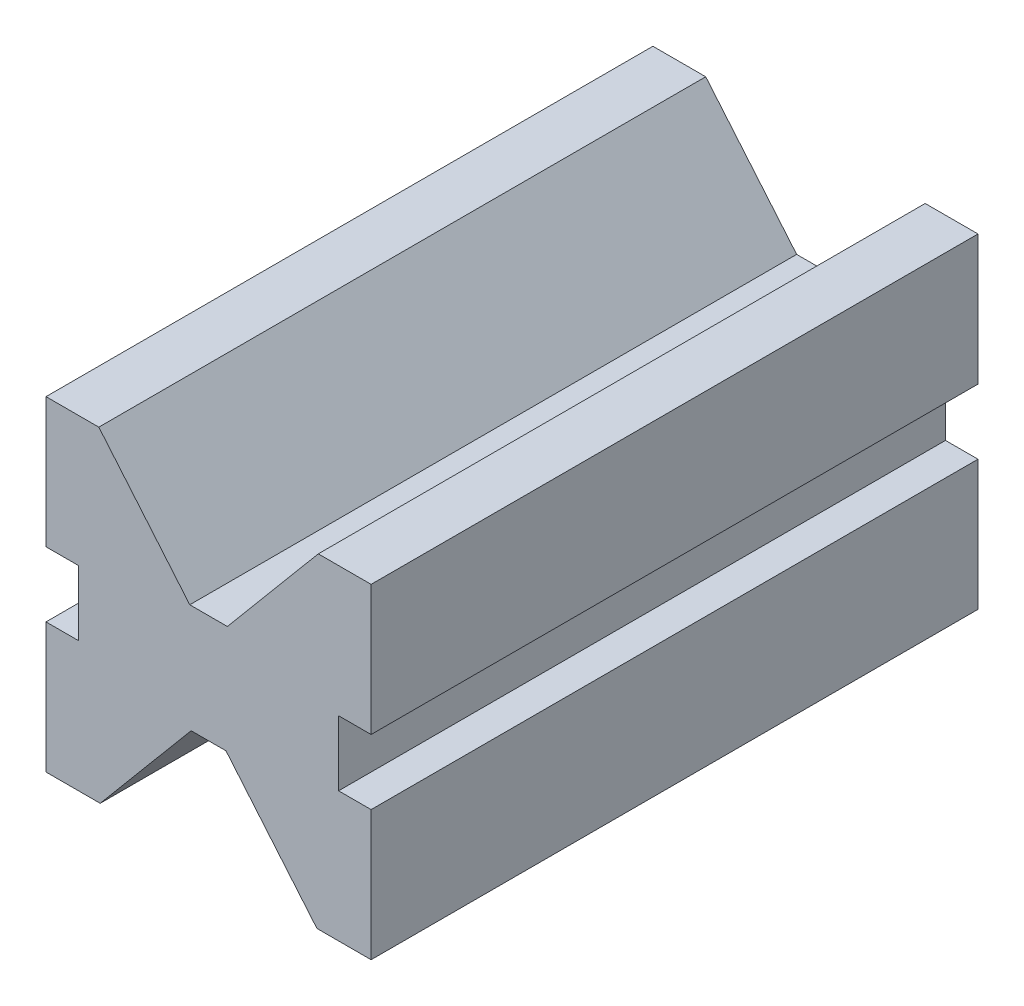
SolidWorks part; units mm, degrees
ref_plane "Front Plane" through (0, 0, 0) normal (0, 0, 1) x (1, 0, 0)
ref_plane "Top Plane" through (0, 0, 0) normal (0, 1, 0) x (1, 0, 0)
ref_plane "Right Plane" through (0, 0, 0) normal (1, 0, 0) x (0, 0, -1)
sketch "Sketch1" plane through (0, 0, 0) normal (0, 0, 1) x (1, 0, 0)
  line L0 (0, 762) -> (0, -762) construction
  line L1 (-88.0874, 254) -> (88.0874, 254)
  line L2 (88.0874, 254) -> (514.35, 762)
  line L3 (-88.0874, 254) -> (-514.35, 762)
  line L4 (514.35, 762) -> (762, 762)
  line L5 (-514.35, 762) -> (-762, 762)
  line L6 (762, 762) -> (762, 152.4)
  line L7 (-762, 762) -> (-762, 152.4)
  line L8 (762, 152.4) -> (609.6, 152.4)
  line L9 (-762, 152.4) -> (-609.6, 152.4)
  line L10 (609.6, 152.4) -> (609.6, -152.4)
  line L11 (-609.6, 152.4) -> (-609.6, -152.4)
  line L12 (609.6, -152.4) -> (762, -152.4)
  line L13 (-609.6, -152.4) -> (-762, -152.4)
  line L14 (762, -152.4) -> (762, -762)
  line L15 (-762, -152.4) -> (-762, -762)
  line L16 (762, -762) -> (508, -762)
  line L17 (-762, -762) -> (-508, -762)
  line L18 (508, -762) -> (81.7374, -254)
  line L19 (-508, -762) -> (-81.7374, -254)
  line L20 (81.7374, -254) -> (-81.7374, -254)
  line L21 (-508, -762) -> (508, -762) construction
  line L22 (0, 762) -> (514.35, 762) construction
  point P6 (0, 254)
  point P24 (0, -254)
  point P27 (0, 0)
  point P30 (638.175, 762)
  dimension "D1" = 508
  dimension "D2" = 1524
  dimension "D3" = 609.6
  dimension "D4" = 609.6
  dimension "D5" = 152.4
  dimension "D6" = 508
  dimension "D7" = 1016
  dimension "D8" = 50
  dimension "D9" = 1028.7
  dimension "D10" = 50
  dimension "D11" = 1524
  dimension "D12" = 1524
extrude "Boss-Extrude1" add sketch "Sketch1" along normal blind 2844.8
equation "\"C\"=112"
equation "\"D1@Boss-Extrude1\"=\"C\""
